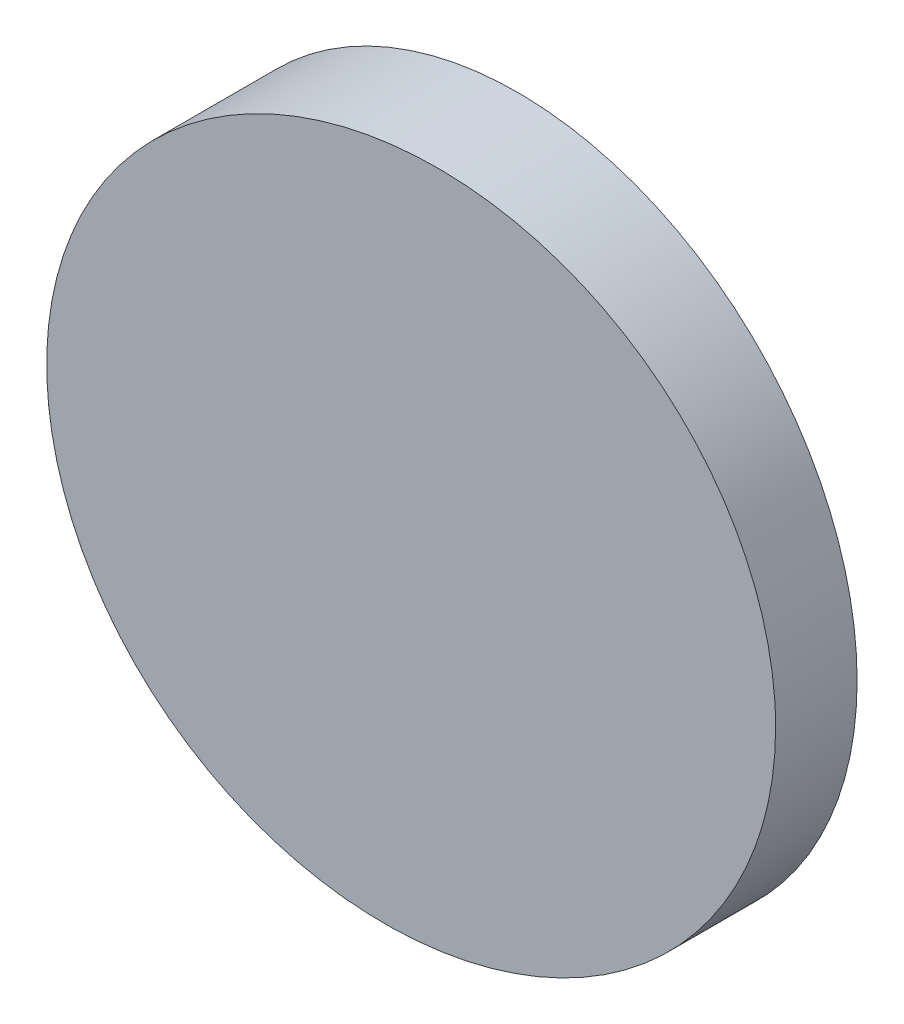
SolidWorks part; units mm, degrees
ref_plane "前视基准面" through (0, 0, 0) normal (0, 0, 1) x (1, 0, 0)
ref_plane "上视基准面" through (0, 0, 0) normal (0, 1, 0) x (1, 0, 0)
ref_plane "右视基准面" through (0, 0, 0) normal (1, 0, 0) x (0, 0, -1)
sketch "草图1" plane through (0, 0, 0) normal (0, 0, 1) x (1, 0, 0)
  circle A0 centre (0, 0) radius 12.5
extrude "凸台-拉伸1" add sketch "草图1" along normal blind 10
sketch "草图2" plane through (0, 0, 0) normal (0, 1, 0) x (1, 0, 0)
  line L0 (12.5, -3) -> (-16.5644, -5.1277)
  line L1 (12.5, -10) -> (12.5, 0) construction
  line L2 (-16.5644, -5.1277) -> (-16.5644, -16.0656)
  line L3 (-16.5644, -16.0656) -> (17.8445, -16.0656)
  line L4 (17.8445, -16.0656) -> (17.8445, -3)
  line L5 (17.8445, -3) -> (12.5, -3)
  line L6 (12.5, 0) -> (-12.5, 0) construction
  dimension "D1" = 4.187
  dimension "D2" = 3
extrude "切除-拉伸1" cut sketch "草图2" against normal mid plane 50
